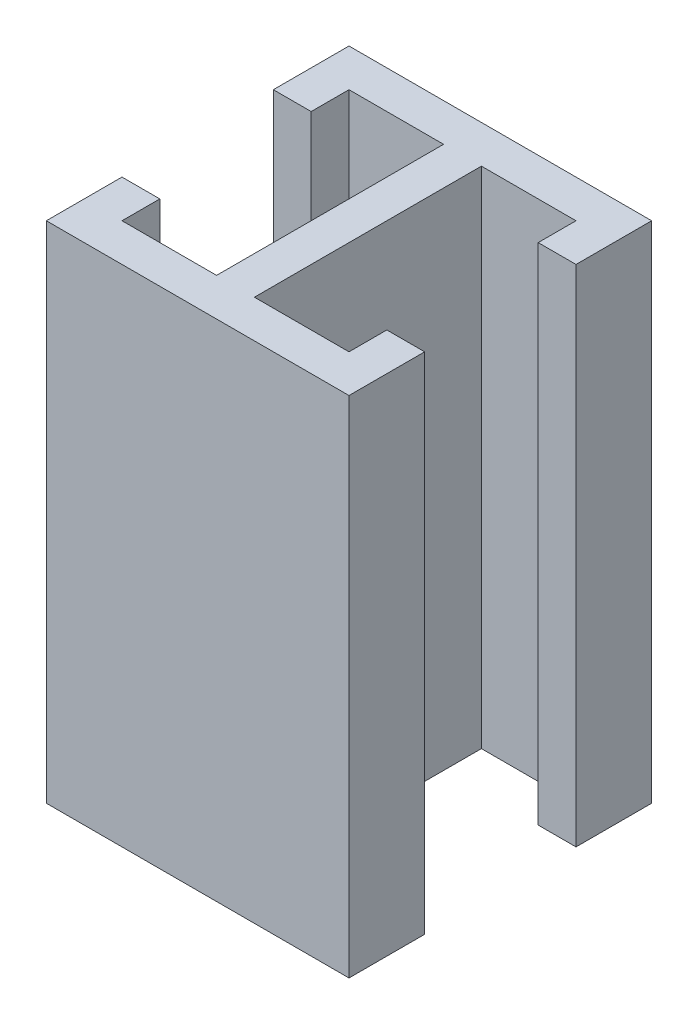
SolidWorks part; units mm, degrees
ref_plane "正面" through (0, 0, 0) normal (0, 0, 1) x (1, 0, 0)
ref_plane "平面" through (0, 0, 0) normal (0, 1, 0) x (1, 0, 0)
ref_plane "右側面" through (0, 0, 0) normal (1, 0, 0) x (0, 0, -1)
sketch "ｽｹｯﾁ5" plane through (0, 0, 0) normal (0, 1, 0) x (1, 0, 0)
  line L1 (0, 0) -> (120, 0)
  line L2 (0, 0) -> (0, 30)
  line L3 (0, 120) -> (120, 120)
  line L4 (120, 0) -> (120, 30)
  line L6 (52.5, 105) -> (15, 105)
  line L7 (52.5, 105) -> (52.5, 15)
  line L8 (52.5, 15) -> (15, 15)
  line L9 (15, 105) -> (15, 90)
  line L11 (15, 90) -> (0, 90)
  line L13 (15, 30) -> (0, 30)
  line L16 (67.5, 105) -> (105, 105)
  line L17 (67.5, 105) -> (67.5, 15)
  line L18 (67.5, 15) -> (105, 15)
  line L19 (105, 105) -> (105, 90)
  line L20 (0, 90) -> (0, 120)
  line L21 (105, 90) -> (120, 90)
  line L23 (105, 30) -> (120, 30)
  line L25 (15, 30) -> (15, 15)
  line L26 (120, 90) -> (120, 120)
  line L27 (105, 30) -> (105, 15)
  point P0 (0, 0)
  point P1 (0, 30)
  point P2 (15.8065, 48.2826)
  point P3 (15, 15)
  point P5 (64.9248, 14.7929)
  point P6 (52.5, 105)
  point P7 (15.8065, 137.9607)
  point P8 (15, 90)
  point P9 (0, 108.5641)
  point P10 (0, 155.4498)
  point P11 (120, 120)
  point P12 (136.7417, 108.5641)
  point P13 (105, 90)
  point P14 (118.8805, 137.9607)
  point P15 (67.5, 105)
  point P16 (84.2744, 14.7929)
  point P17 (105, 15)
  point P18 (118.8805, 48.2826)
  point P19 (120, 30)
  point P20 (136.7417, 0)
  dimension "D1" = 120
  dimension "D2" = 15
  dimension "D3" = 15
  dimension "D4" = 120
  dimension "D5" = 15
  dimension "D6" = 15
  dimension "D7" = 15
  dimension "D8" = 15
  dimension "D9" = 15
  dimension "D10" = 52.5
  dimension "D11" = 30
  dimension "D12" = 30
  dimension "D13" = 30
  dimension "D14" = 30
extrude "ﾎﾞｽ - 押し出し1" add sketch "ｽｹｯﾁ5" along normal blind 200
fillet "ﾌｨﾚｯﾄ1" [suppressed] radius 22.5
fillet "ﾌｨﾚｯﾄ2" [suppressed] radius 7.5
equation "\"C\" = 30"
equation "\"B\" = 15"
equation "\"A\"= 15"
equation "\"D2@ｽｹｯﾁ5\"=\"B\""
equation "\"D3@ｽｹｯﾁ5\"=\"B\""
equation "\"D5@ｽｹｯﾁ5\"=\"B\""
equation "\"D6@ｽｹｯﾁ5\"=\"B\""
equation "\"D7@ｽｹｯﾁ5\"=\"B\""
equation "\"D8@ｽｹｯﾁ5\"=\"B\""
equation "\"D9@ｽｹｯﾁ5\"=\"A\""
equation "\"D11@ｽｹｯﾁ5\"=\"C\""
equation "\"D12@ｽｹｯﾁ5\"=\"C\""
equation "\"D13@ｽｹｯﾁ5\"=\"C\""
equation "\"D14@ｽｹｯﾁ5\"=\"C\""
equation "\"D10@ｽｹｯﾁ5\"=60 - \"A\"/2"
equation "\"D1@ﾌｨﾚｯﾄ1\"=\"B\"/2*3"
equation "\"D1@ﾌｨﾚｯﾄ2\"=\"B\"/2"
